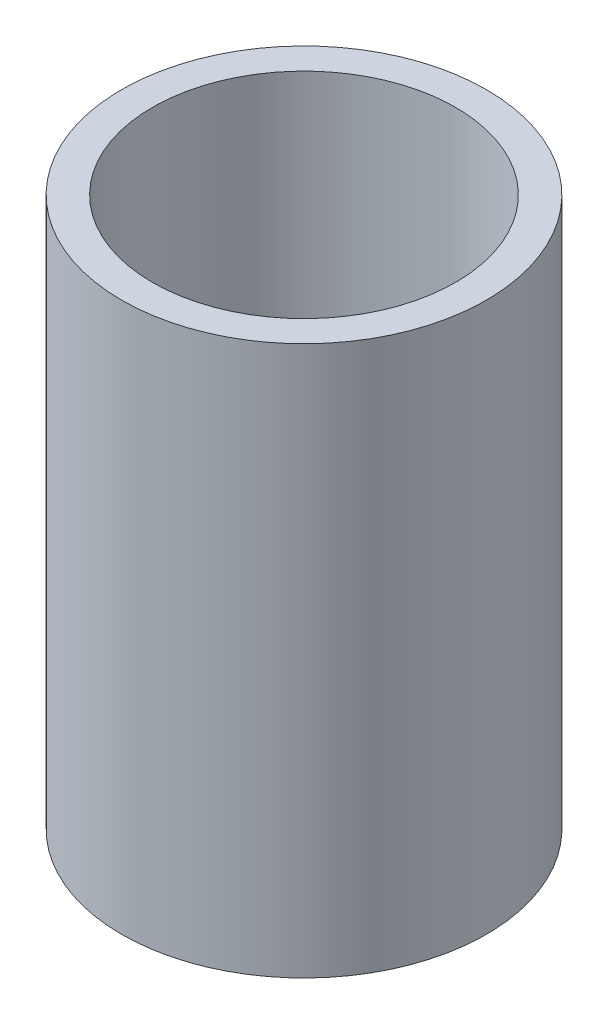
SolidWorks part; units mm, degrees
material "6061-T6 (SS)"
ref_plane "Front Plane" through (0, 0, 0) normal (0, 0, 1) x (1, 0, 0)
ref_plane "Top Plane" through (0, 0, 0) normal (0, 1, 0) x (1, 0, 0)
ref_plane "Right Plane" through (0, 0, 0) normal (1, 0, 0) x (0, 0, -1)
sketch "Sketch1" plane through (0, 0, 0) normal (0, 1, 0) x (1, 0, 0)
  circle A0 centre (0, 0) radius 21.082
  circle A1 centre (0, 0) radius 17.526
  dimension "D1" = 42.164
  dimension "D2" = 35.052
extrude "Boss-Extrude1" add sketch "Sketch1" along normal blind 63.5
